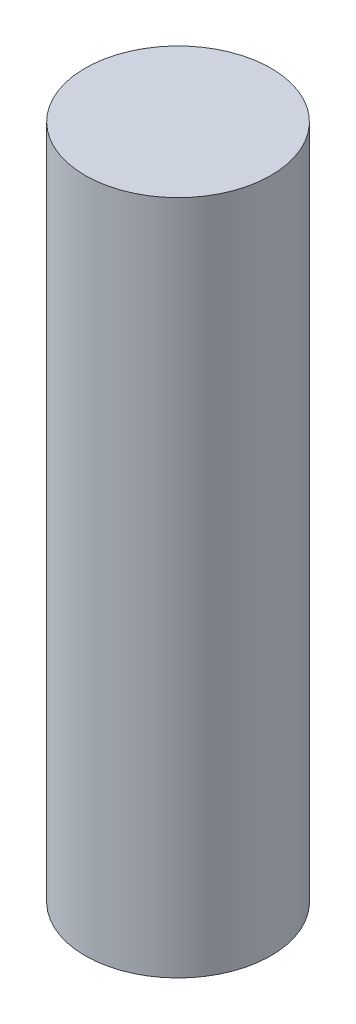
SolidWorks part; units mm, degrees
ref_plane "Front Plane" through (0, 0, 0) normal (0, 0, 1) x (1, 0, 0)
ref_plane "Top Plane" through (0, 0, 0) normal (0, 1, 0) x (1, 0, 0)
ref_plane "Right Plane" through (0, 0, 0) normal (1, 0, 0) x (0, 0, -1)
sketch "Sketch1" plane through (0, 0, 0) normal (0, 1, 0) x (1, 0, 0)
  circle A0 centre (0, 0) radius 12.375
  dimension "D1" = 24.75
extrude "Boss-Extrude1" add sketch "Sketch1" along normal blind 90
